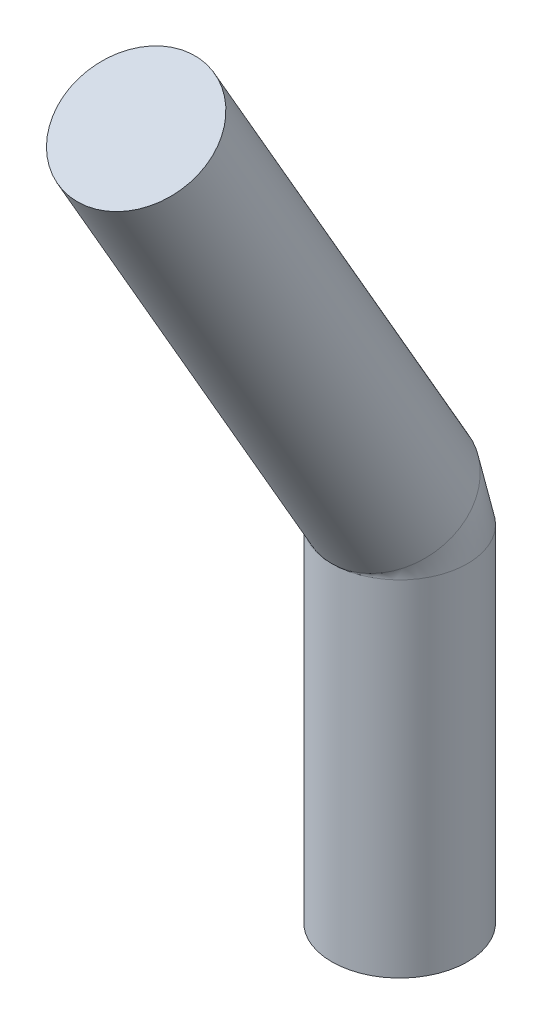
SolidWorks part; units mm, degrees
ref_plane "Front Plane" through (0, 0, 0) normal (0, 0, 1) x (1, 0, 0)
ref_plane "Top Plane" through (0, 0, 0) normal (0, 1, 0) x (1, 0, 0)
ref_plane "Right Plane" through (0, 0, 0) normal (1, 0, 0) x (0, 0, -1)
sketch "Sketch23" plane through (0, 0, 0) normal (0, 1, 0) x (1, 0, 0)
  circle A0 centre (0, 0) radius 0.6
  dimension "D1" = 1.2
sketch "Sketch24" plane through (0, 0, 0) normal (1, 0, 0) x (0, 0, -1)
  line L0 (0, 0) -> (0, 0.5)
  line L1 (0, 0.66) -> (0, -0.66) construction
  line L2 (-0.0804, 0.8) -> (-2.3304, 4.6971)
  arc A0 (0, 0.5) -> (-0.0804, 0.8) centre (-0.6, 0.5) ccw
  dimension "D1" = 0.5
  dimension "D2" = 0.6
  dimension "D3" = 30
  dimension "D4" = 4.5
sweep "Sweep4" add profiles "Sketch23" path "Sketch24"
sketch "Sketch25" plane through (0, 0, 0) normal (0, -1, 0) x (-1, 0, 0)
  circle A0 centre (0, 0) radius 0.6
  dimension "D1" = 1.2
extrude "Boss-Extrude2" add sketch "Sketch25" along normal blind 2.55
sketch "Sketch28" plane through (0, 4.5319, 2.6165) normal (0, 0.866, 0.5) x (1, 0, 0)
  line L0 (0, 0.3304) -> (0.6, 0.3304)
  circle A0 centre (0, 0.3304) radius 0.6 construction
